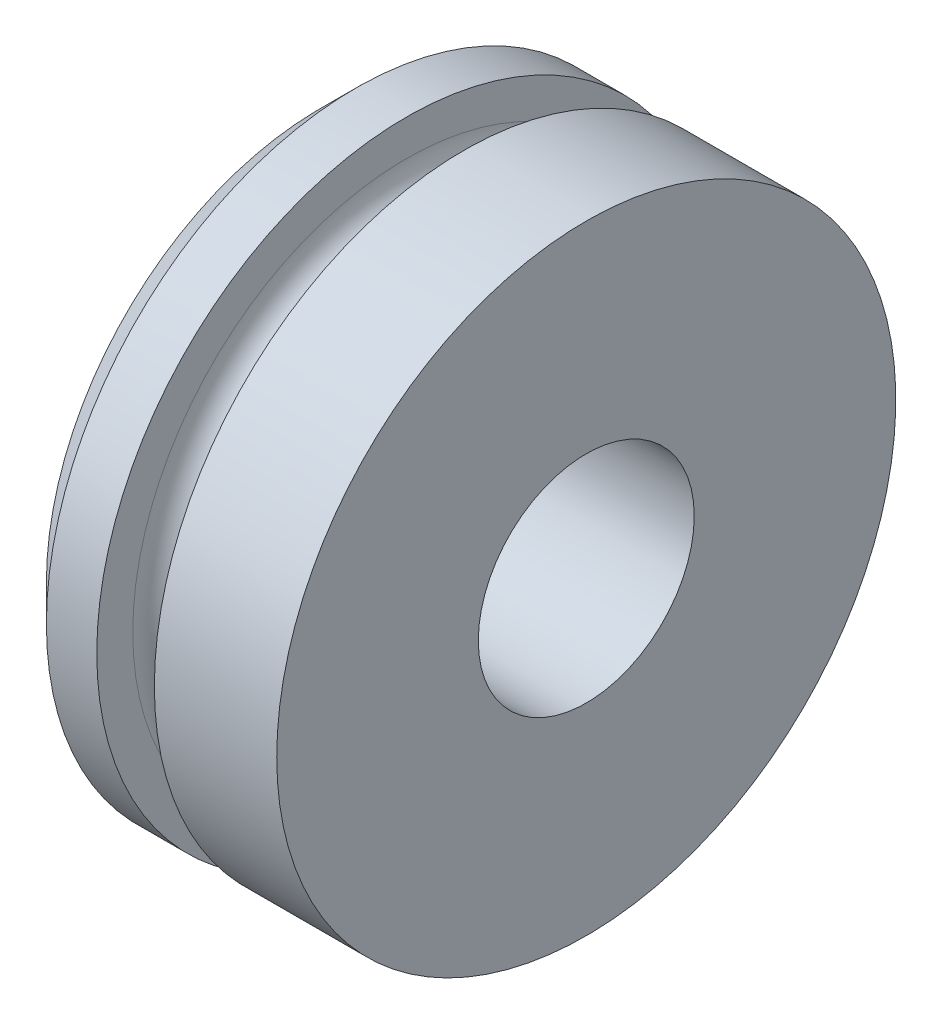
SolidWorks part; units mm, degrees
material "6061-T6 (SS)"
ref_plane "Front Plane" through (0, 0, 0) normal (0, 0, 1) x (1, 0, 0)
ref_plane "Top Plane" through (0, 0, 0) normal (0, 1, 0) x (1, 0, 0)
ref_plane "Right Plane" through (0, 0, 0) normal (1, 0, 0) x (0, 0, -1)
sketch "Sketch1" plane through (0, 0, 0) normal (0, 0, 1) x (1, 0, 0)
  line L0 (0, 9.525) -> (23.495, 9.525)
  line L1 (0, 0) -> (23.495, 0) construction
  line L2 (0, 0) -> (0, 27.305)
  line L3 (0, 27.305) -> (7.62, 27.305)
  line L4 (7.62, 24.13) -> (7.62, 27.305)
  line L6 (12.7, 24.13) -> (12.7, 27.305)
  line L7 (12.7, 27.305) -> (23.495, 27.305)
  line L8 (23.495, 0) -> (23.495, 27.305)
  line L9 (10.16, 21.59) -> (10.16, 0) construction
  arc A0 (7.62, 24.13) -> (12.7, 24.13) centre (10.16, 24.13) ccw
  dimension "D1" = 2.54
  dimension "D3" = 27.305
  dimension "D4" = 3.175
  dimension "D2" = 7.62
  dimension "D6" = 9.525
  dimension "D7" = 21.59
  dimension "D5" = 23.495
revolve "Revolve1" add sketch "Sketch1" angle 360 about L1
chamfer "Chamfer1" distance 3.175 angle 45 1 edges at (0, 0, 27.305)
equation "\"D4@Sketch1\"=.125"
